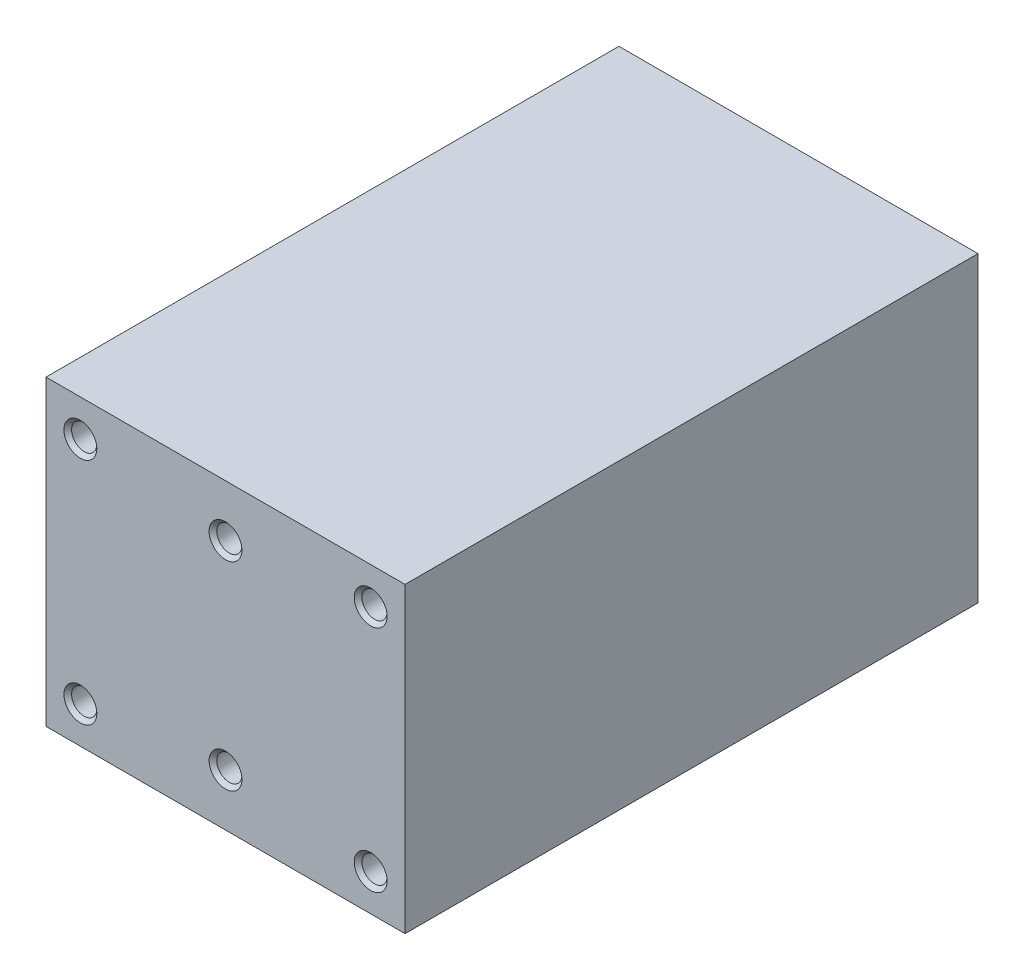
SolidWorks part; units mm, degrees
ref_plane "Płaszczyzna przednia" through (0, 0, 0) normal (0, 0, 1) x (1, 0, 0)
ref_plane "Płaszczyzna górna" through (0, 0, 0) normal (0, 1, 0) x (1, 0, 0)
ref_plane "Płaszczyzna prawa" through (0, 0, 0) normal (1, 0, 0) x (0, 0, -1)
sketch "Szkic1" plane through (0, 0, 0) normal (0, 0, 1) x (1, 0, 0)
  line L1 (0, 0) -> (47, 0)
  line L2 (0, 0) -> (0, 39.6)
  line L3 (0, 39.6) -> (47, 39.6)
  line L4 (47, 0) -> (47, 39.6)
  dimension "D1" = 39.6
  dimension "D2" = 47
extrude "Dodanie-wyciągnięcie1" add sketch "Szkic1" along normal blind 75
sketch "Szkic2" plane through (0, 0, 75) normal (0, 0, 1) x (1, 0, 0)
  line L0 (23.5, 34.8) -> (23.5, 4.8) construction
  line L1 (4.5, 4.8) -> (42.5, 4.8) construction
  line L2 (4.5, 4.8) -> (4.5, 34.8) construction
  line L3 (4.5, 34.8) -> (42.5, 34.8) construction
  line L4 (42.5, 4.8) -> (42.5, 34.8) construction
  line L5 (0, 39.6) -> (0, 0) construction
  line L6 (0, 19.8) -> (47, 19.8) construction
  line L7 (47, 0) -> (47, 39.6) construction
  line L9 (23.5, 39.6) -> (23.5, 0) construction
  line L10 (47, 39.6) -> (0, 39.6) construction
  line L11 (0, 0) -> (47, 0) construction
  circle A0 centre (4.5, 34.8) radius 1.65
  circle A1 centre (42.5, 34.8) radius 1.65
  circle A2 centre (42.5, 4.8) radius 1.65
  circle A3 centre (4.5, 4.8) radius 1.65
  circle A4 centre (23.5, 32.8) radius 1.65
  circle A5 centre (23.5, 6.8) radius 1.65
  point P14 (23.5, 19.8)
  point P21 (4.5, 19.8)
  dimension "D3" = 26
  dimension "D4" = 13
  dimension "D5" = 3.3
  dimension "D1" = 38
  dimension "D2" = 30
hole_wizard "Otwór gwintowany M4x0.72" positions "Szkic5" profile "Szkic6" tap size "M4x0.7" standard "Ansi Metric"
sketch "Szkic5" plane through (0, 0, 75) normal (0, 0, 1) x (1, 0, 0)
  point P0 (4.5, 34.8)
  point P3 (23.5, 32.8)
  point P6 (42.5, 34.8)
  point P9 (42.5, 4.8)
  point P12 (23.5, 6.8)
  point P15 (4.5, 4.8)
sketch "Szkic6" plane through (4.5, 34.8, 75) normal (1, 0, 0) x (0, -1, 0)
  line L0 (0, 0) -> (0, 15.9914)
  line L1 (0, 15.9914) -> (1.65, 15)
  line L2 (1.65, 15) -> (1.65, 0)
  line L5 (1.65, 0) -> (0, 0)
  line L10 (0, 15.9914) -> (-1.65, 15) construction
  line L11 (0, -6.35) -> (0, 107.95) construction
  dimension "Średnica wiertła gwintu" = 3.3
  dimension "Głębokość otworu gwintowanego" = 15
  dimension "Kąt wiertła" = 118
cosmetic thread "Gwint otworu1"
cosmetic thread "Gwint otworu2"
cosmetic thread "Gwint otworu3"
cosmetic thread "Gwint otworu4"
cosmetic thread "Gwint otworu5"
cosmetic thread "Gwint otworu6"
chamfer "Sfazowanie1" distance 0.5 angle 45 6 edges at (6.15, 4.8, 75) (25.15, 6.8, 75) (44.15, 4.8, 75) (44.15, 34.8, 75) (25.15, 32.8, 75) (6.15, 34.8, 75)
